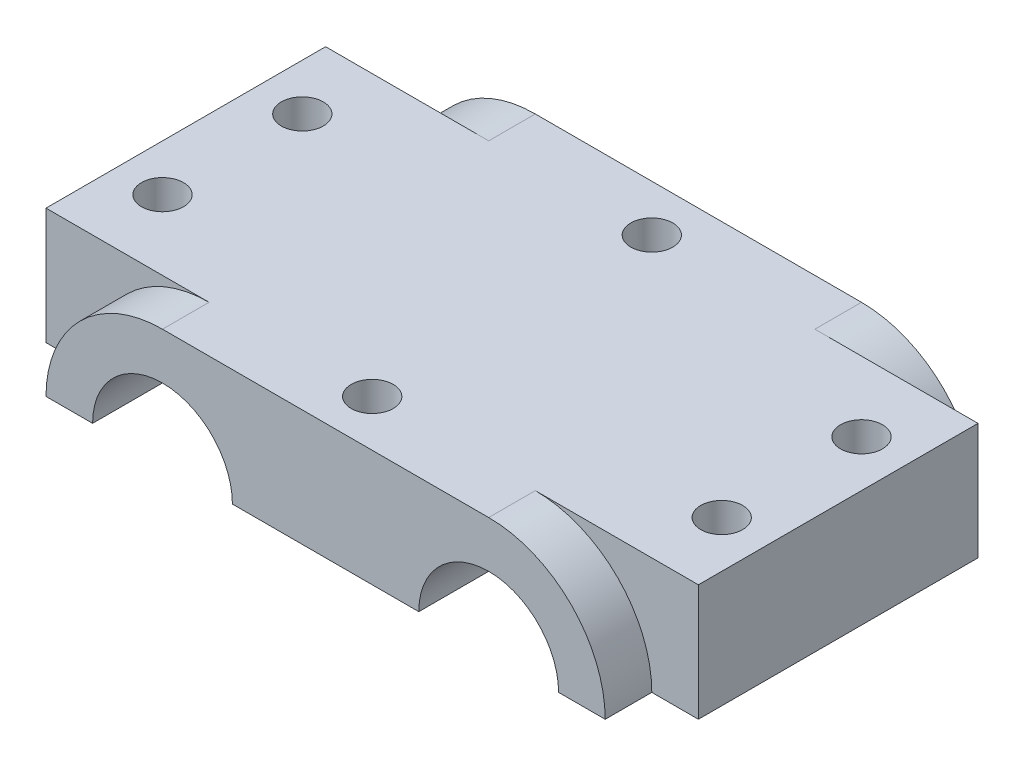
SolidWorks part; units mm, degrees
ref_plane "Front Plane" through (0, 0, 0) normal (0, 0, 1) x (1, 0, 0)
ref_plane "Top Plane" through (0, 0, 0) normal (0, 1, 0) x (1, 0, 0)
ref_plane "Right Plane" through (0, 0, 0) normal (1, 0, 0) x (0, 0, -1)
sketch "Sketch2" plane through (0, 0, 0) normal (0, 0, 1) x (1, 0, 0)
  line L0 (0, 0) -> (0, 12.5)
  line L1 (0, 12.5) -> (70, 12.5)
  line L2 (0, 0) -> (10, 0)
  line L3 (25, 0) -> (45, 0)
  line L5 (70, 0) -> (60, 0)
  line L6 (70, 0) -> (70, 12.5)
  arc A0 (10, 0) -> (25, 0) centre (17.5, 0) cw
  arc A1 (60, 0) -> (45, 0) centre (52.5, 0) ccw
extrude "Boss-Extrude1" add sketch "Sketch2" along normal blind 30
sketch "Sketch3" plane through (0, 0, 30) normal (0, 0, 1) x (1, 0, 0)
  line L0 (0, 0) -> (10, 0) construction
  line L1 (70, 12.5) -> (0, 12.5) construction
  line L4 (17.5, 12.5) -> (52.5, 12.5)
  line L5 (5, 0) -> (10, 0)
  line L6 (25, 0) -> (45, 0)
  line L7 (65, 0) -> (60, 0)
  arc A0 (5, 0) -> (17.5, 12.5) centre (17.5, 0) cw
  arc A1 (10, 0) -> (25, 0) centre (17.5, 0) cw
  arc A2 (25, 0) -> (10, 0) centre (17.5, 0) ccw construction
  arc A3 (65, 0) -> (52.5, 12.5) centre (52.5, 0) ccw
  arc A4 (60, 0) -> (45, 0) centre (52.5, 0) ccw
extrude "Boss-Extrude2" add sketch "Sketch3" along normal blind 5
sketch "Sketch4" plane through (0, 0, 0) normal (0, 0, -1) x (-1, 0, 0)
  line L0 (-25, 0) -> (-45, 0) construction
  line L1 (-60, 0) -> (-70, 0) construction
  line L2 (-70, 12.5) -> (0, 12.5) construction
  line L3 (-65, 0) -> (-60, 0)
  line L5 (-52.5, 12.5) -> (-17.5, 12.5)
  line L6 (-45, 0) -> (-25, 0)
  line L7 (-5, 0) -> (-10, 0)
  arc A0 (-60, 0) -> (-45, 0) centre (-52.5, 0) cw
  arc A1 (-65, 0) -> (-52.5, 12.5) centre (-52.5, 0) cw
  arc A2 (-10, 0) -> (-25, 0) centre (-17.5, 0) ccw
  arc A3 (-5, 0) -> (-17.5, 12.5) centre (-17.5, 0) ccw
extrude "Boss-Extrude3" add sketch "Sketch4" along normal blind 5
sketch "Sketch5" plane through (0, 12.5, 0) normal (0, 1, 0) x (1, 0, 0)
  circle A0 centre (35, 0) radius 2.25
  circle A1 centre (35, -30) radius 2.25
  circle A2 centre (65, -7.5) radius 2.25
  circle A3 centre (65, -22.5) radius 2.25
  circle A4 centre (5, -22.5) radius 2.25
  circle A5 centre (5, -7.5) radius 2.25
  point P14 (35, -30)
  point P25 (5, -22.5)
  point P28 (5, -7.5)
extrude "Cut-Extrude1" cut sketch "Sketch5" against normal blind 12.5 contours A5 | A0 | A2 | A3 | A1 | A4
